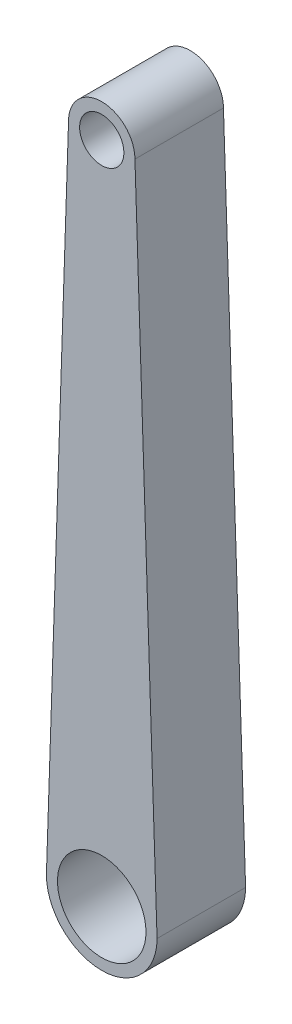
SolidWorks part; units mm, degrees
ref_plane "Front Plane" through (0, 0, 0) normal (0, 0, 1) x (1, 0, 0)
ref_plane "Top Plane" through (0, 0, 0) normal (0, 1, 0) x (1, 0, 0)
ref_plane "Right Plane" through (0, 0, 0) normal (1, 0, 0) x (0, 0, -1)
sketch "Sketch1" plane through (0, 0, 0) normal (0, 0, 1) x (1, 0, 0)
  line L0 (0, 245.2275) -> (0, 235.2275) construction
  line L1 (15, 245.2275) -> (25, -54.7725)
  line L2 (-15, 245.2275) -> (-25, -54.7725)
  line L3 (0, -42.2725) -> (0, -54.7725) construction
  arc A0 (15, 245.2275) -> (-15, 245.2275) centre (0, 245.2275) ccw
  arc A1 (-25, -54.7725) -> (25, -54.7725) centre (0, -54.7725) ccw
  circle A2 centre (0, 245.2275) radius 10
  circle A3 centre (0, -54.7725) radius 20
  dimension "D1" = 20
  dimension "D2" = 30
  dimension "D3" = 40
  dimension "D4" = 50
  dimension "D5" = 300
extrude "Boss-Extrude1" add sketch "Sketch1" along normal blind 40 contours L2 A1 L1 A0 A3 A2
